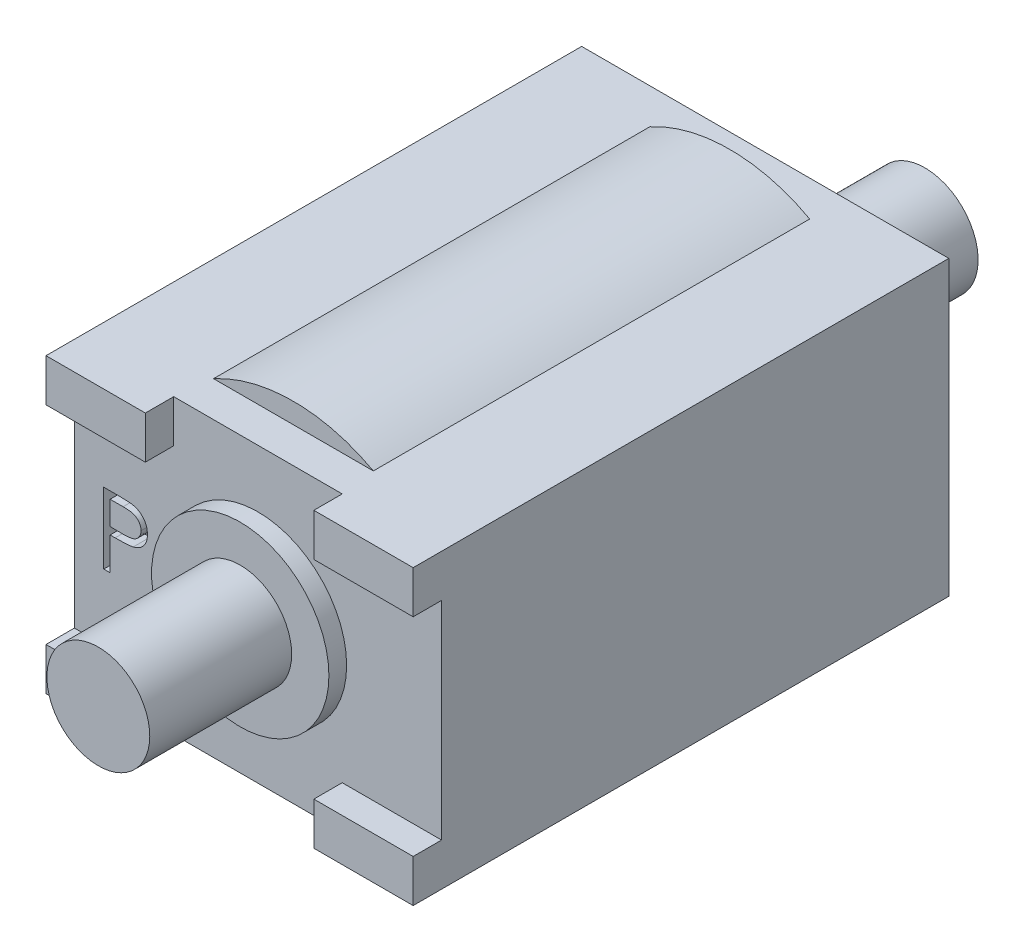
SolidWorks part; units mm, degrees
ref_plane "Front Plane" through (0, 0, 0) normal (0, 0, 1) x (1, 0, 0)
ref_plane "Top Plane" through (0, 0, 0) normal (0, 1, 0) x (1, 0, 0)
ref_plane "Right Plane" through (0, 0, 0) normal (1, 0, 0) x (0, 0, -1)
sketch "Sketch1" plane through (0, 0, 0) normal (0, 0, 1) x (1, 0, 0)
  line L0 (-5.175, -4.125) -> (5.175, -4.125)
  line L1 (-5.175, -4.125) -> (-5.175, 4.125)
  line L2 (5.175, -4.125) -> (5.175, 4.125)
  line L3 (-5.175, 4.125) -> (5.175, 4.125)
  line L4 (-5.175, -4.125) -> (5.175, 4.125) construction
  line L5 (5.175, -4.125) -> (-5.175, 4.125) construction
  point P1 (0, 0)
  dimension "D1" = 8.25
  dimension "D2" = 10.35
extrude "Boss-Extrude1" add sketch "Sketch1" along normal blind 14.3
sketch "Sketch2" plane through (0, 0, 14.3) normal (0, 0, 1) x (1, 0, 0)
  circle A0 centre (0, 0) radius 2.5
  dimension "D1" = 5
extrude "Boss-Extrude2" add sketch "Sketch2" along normal blind 0.5
sketch "Sketch3" plane through (0, 0, 14.3) normal (0, 0, 1) x (1, 0, 0)
  circle A0 centre (0, 0) radius 1.45
  dimension "D1" = 2.9
extrude "Boss-Extrude3" add sketch "Sketch3" along normal blind 4.5
sketch "Sketch4" plane through (0, 0, 14.3) normal (0, 0, 1) x (1, 0, 0)
  line L0 (0, 0) -> (0, 1.8465) construction
  line L1 (-5.175, 4.125) -> (-2.375, 4.125)
  line L2 (-5.175, 4.125) -> (-5.175, 2.925)
  line L3 (-5.175, 2.925) -> (-2.375, 2.925)
  line L4 (-2.375, 4.125) -> (-2.375, 2.925)
  line L9 (0, 0) -> (2.0189, 0) construction
  line L10 (5.175, 2.925) -> (2.375, 2.925)
  line L11 (2.375, 4.125) -> (2.375, 2.925)
  line L12 (5.175, 4.125) -> (2.375, 4.125)
  line L13 (5.175, 4.125) -> (5.175, 2.925)
  line L14 (-5.175, -2.925) -> (-2.375, -2.925)
  line L15 (-2.375, -4.125) -> (-2.375, -2.925)
  line L16 (-5.175, -4.125) -> (-2.375, -4.125)
  line L17 (-5.175, -4.125) -> (-5.175, -2.925)
  line L18 (5.175, -4.125) -> (5.175, -2.925)
  line L19 (5.175, -4.125) -> (2.375, -4.125)
  line L20 (2.375, -4.125) -> (2.375, -2.925)
  line L21 (5.175, -2.925) -> (2.375, -2.925)
  dimension "D1" = 1.2
  dimension "D2" = 2.8
extrude "Boss-Extrude4" add sketch "Sketch4" along normal blind 0.8
sketch "Sketch5" plane through (0, 0, 14.3) normal (0, 0, 1) x (1, 0, 0)
  text T0 "P" font "Century Gothic" height 2
extrude "Cut-Extrude1" cut sketch "Sketch5" against normal blind 0.5
sketch "Sketch6" plane through (0, 0, 0) normal (0, 0, -1) x (-1, 0, 0)
  circle A0 centre (0, 0) radius 1.5
  dimension "D1" = 3
extrude "Boss-Extrude5" add sketch "Sketch6" along normal blind 4.5
sketch "Sketch7" plane through (0, 0, 0) normal (0, 0, -1) x (-1, 0, 0)
  circle A0 centre (0, 0) radius 1.9
  dimension "D1" = 3.8
extrude "Boss-Extrude6" add sketch "Sketch7" along normal blind 0.3
sketch "Sketch8" plane through (0, 0, 0) normal (0, 0, -1) x (-1, 0, 0)
  text T0 "m" font "Century Gothic" height 2
extrude "Cut-Extrude2" cut sketch "Sketch8" against normal blind 0.5
sketch "Sketch9" plane through (0, 0, 0) normal (0, 0, -1) x (-1, 0, 0)
  circle A0 centre (0, 0) radius 4.7
  dimension "D1" = 9.4
extrude "Boss-Extrude7" add sketch "Sketch9" against normal offset from surface (12.3 mm away) 1 from offset 1 up to face at (0, 0, 14.3)
